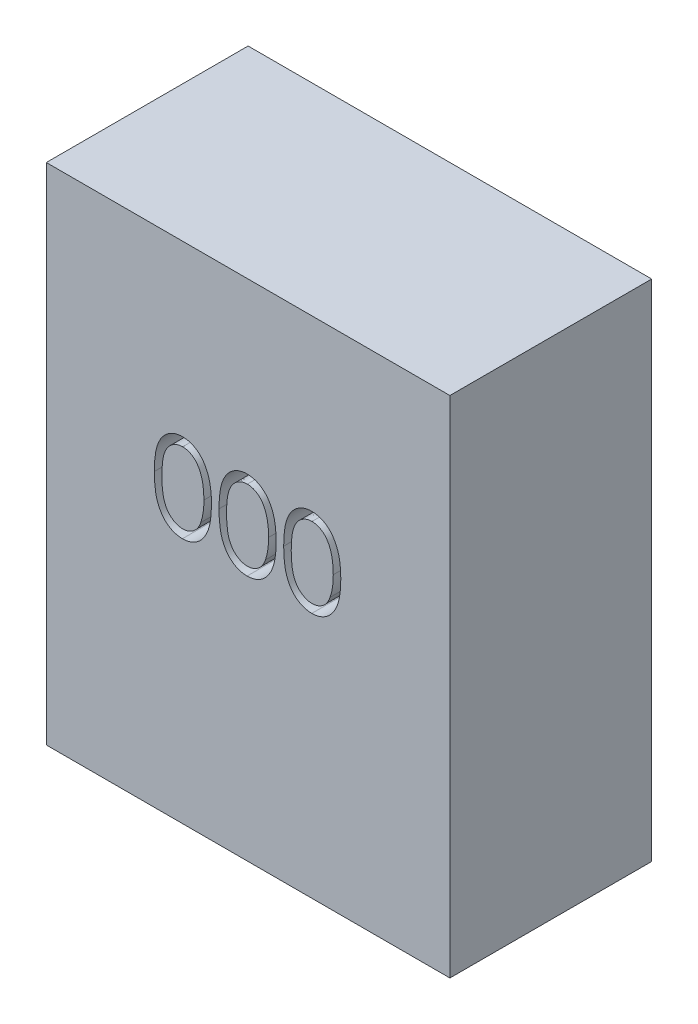
SolidWorks part; units mm, degrees
ref_plane "Front Plane" through (0, 0, 0) normal (0, 0, 1) x (1, 0, 0)
ref_plane "Top Plane" through (0, 0, 0) normal (0, 1, 0) x (1, 0, 0)
ref_plane "Right Plane" through (0, 0, 0) normal (1, 0, 0) x (0, 0, -1)
sketch "Sketch1" plane through (0, 0, 0) normal (0, 0, 1) x (1, 0, 0)
  line L1 (-12, 15) -> (12, 15)
  line L2 (-12, 15) -> (-12, -15)
  line L3 (-12, -15) -> (12, -15)
  line L4 (12, 15) -> (12, -15)
  dimension "D1" = 24
  dimension "D2" = 12
  dimension "D3" = 30
  dimension "D4" = 15
extrude "Boss-Extrude1" add sketch "Sketch1" along normal blind 12
sketch "Sketch2" plane through (0, 0, 12) normal (0, 0, 1) x (1, 0, 0)
  line L0 (-12, -0.1995) -> (12, -0.1995) construction
  line L1 (-12, 15) -> (-12, -15) construction
  line L2 (12, -15) -> (12, 15) construction
  text T0 "000" font "Century Gothic" height 5
extrude "Cut-Extrude1" cut sketch "Sketch2" against normal blind 2
